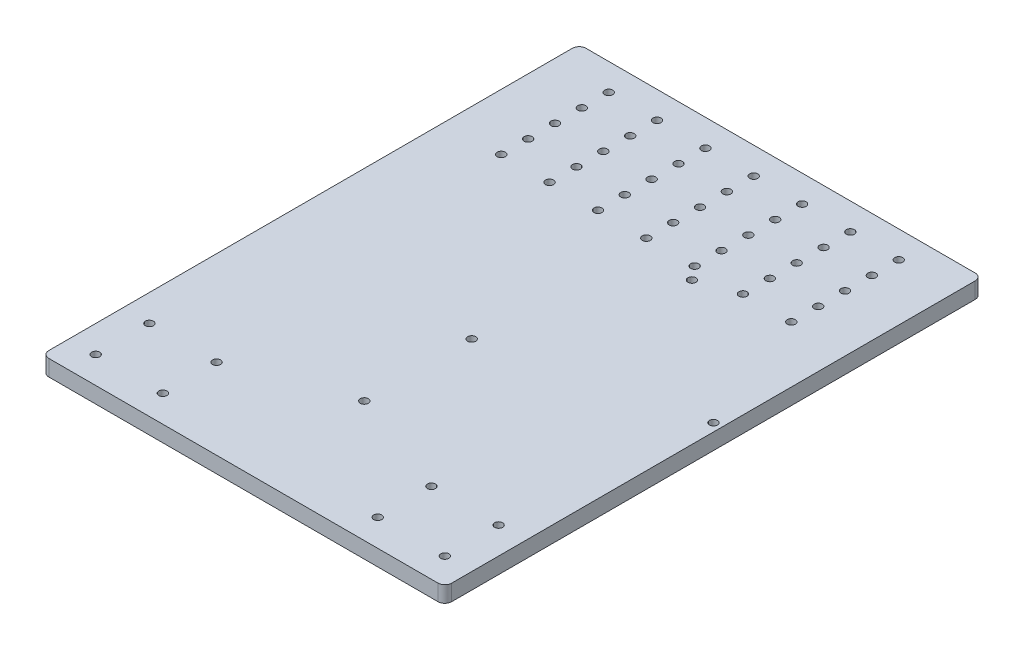
SolidWorks part; units mm, degrees
ref_plane "Front Plane" through (0, 0, 0) normal (0, 0, 1) x (1, 0, 0)
ref_plane "Top Plane" through (0, 0, 0) normal (0, 1, 0) x (1, 0, 0)
ref_plane "Right Plane" through (0, 0, 0) normal (1, 0, 0) x (0, 0, -1)
sketch "Sketch1" plane through (0, 0, 0) normal (0, 1, 0) x (1, 0, 0)
  line L0 (75, 200) -> (75, 0) construction
  line L1 (2.54, 0) -> (147.46, 0)
  line L2 (0, 2.54) -> (0, 197.46)
  line L3 (2.54, 200) -> (147.46, 200)
  line L4 (150, 2.54) -> (150, 197.46)
  line L5 (0, 155) -> (150, 155) construction
  line L6 (0, 165) -> (150, 165) construction
  line L7 (0, 175) -> (150, 175) construction
  line L8 (0, 185) -> (150, 185) construction
  arc A0 (150, 197.46) -> (147.46, 200) centre (147.46, 197.46) ccw
  arc A1 (147.46, 0) -> (150, 2.54) centre (147.46, 2.54) ccw
  arc A2 (2.54, 0) -> (0, 2.54) centre (2.54, 2.54) cw
  arc A3 (2.54, 200) -> (0, 197.46) centre (2.54, 197.46) ccw
  circle A4 centre (10, 30) radius 1.5
  circle A5 centre (35, 30) radius 1.5
  circle A6 centre (35, 10) radius 1.5
  circle A7 centre (10, 10) radius 1.5
  circle A8 centre (140, 10) radius 1.5
  circle A9 centre (115, 10) radius 1.5
  circle A10 centre (115, 30) radius 1.5
  circle A11 centre (140, 30) radius 1.5
  circle A12 centre (75, 150) radius 1.5
  circle A13 centre (39, 150) radius 1.5
  circle A14 centre (21, 150) radius 1.5
  circle A15 centre (57, 150) radius 1.5
  circle A16 centre (93, 150) radius 1.5
  circle A17 centre (111, 150) radius 1.5
  circle A18 centre (129, 150) radius 1.5
  circle A19 centre (129, 160) radius 1.5
  circle A20 centre (111, 160) radius 1.5
  circle A21 centre (93, 160) radius 1.5
  circle A22 centre (75, 160) radius 1.5
  circle A23 centre (57, 160) radius 1.5
  circle A24 centre (39, 160) radius 1.5
  circle A25 centre (21, 160) radius 1.5
  circle A26 centre (129, 170) radius 1.5
  circle A27 centre (111, 170) radius 1.5
  circle A28 centre (93, 170) radius 1.5
  circle A29 centre (75, 170) radius 1.5
  circle A30 centre (57, 170) radius 1.5
  circle A31 centre (39, 170) radius 1.5
  circle A32 centre (21, 170) radius 1.5
  circle A33 centre (129, 180) radius 1.5
  circle A34 centre (111, 180) radius 1.5
  circle A35 centre (93, 180) radius 1.5
  circle A36 centre (75, 180) radius 1.5
  circle A37 centre (57, 180) radius 1.5
  circle A38 centre (39, 180) radius 1.5
  circle A39 centre (21, 180) radius 1.5
  circle A40 centre (129, 190) radius 1.5
  circle A41 centre (111, 190) radius 1.5
  circle A42 centre (93, 190) radius 1.5
  circle A43 centre (75, 190) radius 1.5
  circle A44 centre (57, 190) radius 1.5
  circle A45 centre (39, 190) radius 1.5
  circle A46 centre (21, 190) radius 1.5
  circle A47 centre (75, 45) radius 1.5
  circle A49 centre (75, 85) radius 1.5
  circle A51 centre (147, 103) radius 1.5
  circle A52 centre (97, 145) radius 1.5
  point P11 (0, 0)
  dimension "D1" = 2.54
  dimension "D4" = 3
  dimension "D9" = 3
  dimension "D10" = 18
  dimension "D11" = 18
  dimension "D12" = 18
  dimension "D13" = 50
  dimension "D18" = 3
  dimension "D19" = 45
  dimension "D20" = 3
  dimension "D21" = 85
  dimension "D22" = 3
  dimension "D23" = 3
  dimension "D24" = 18
  dimension "D25" = 3
  dimension "D26" = 50
  dimension "D27" = 42
  dimension "D2" = 200
  dimension "D3" = 150
  dimension "D5" = 20
  dimension "D6" = 25
  dimension "D7" = 10
  dimension "D8" = 10
  dimension "D14" = 5
  dimension "D15" = 5
  dimension "D16" = 5
  dimension "D17" = 5
extrude "Boss-Extrude1" add sketch "Sketch1" along normal blind 6
